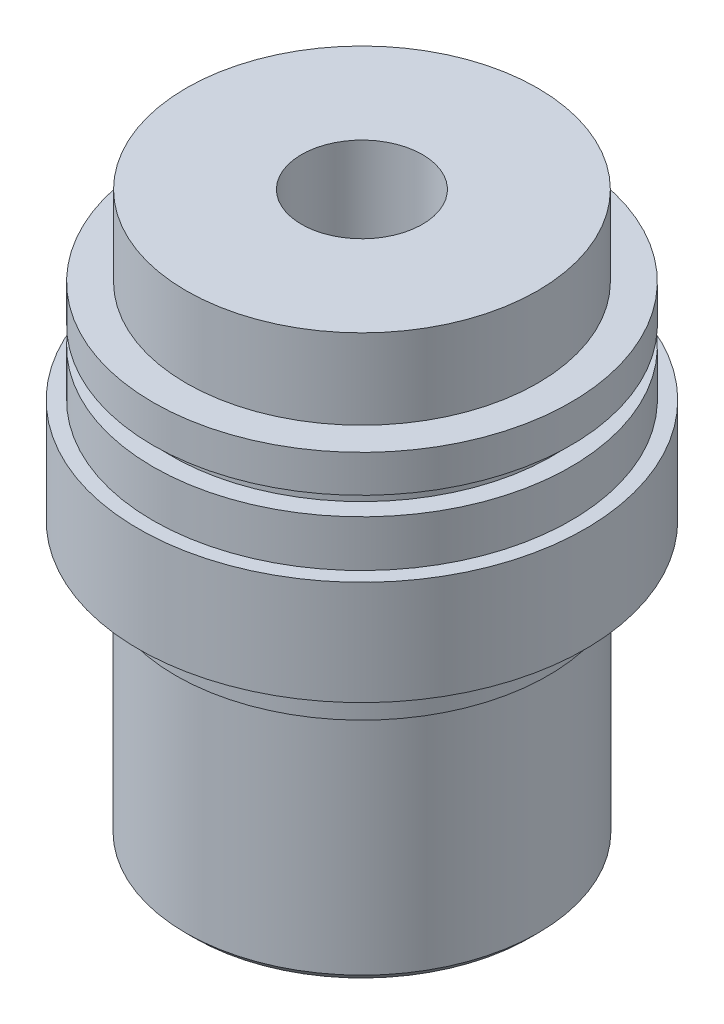
SolidWorks part; units mm, degrees
ref_plane "Front Plane" through (0, 0, 0) normal (0, 0, 1) x (1, 0, 0)
ref_plane "Top Plane" through (0, 0, 0) normal (0, 1, 0) x (1, 0, 0)
ref_plane "Right Plane" through (0, 0, 0) normal (1, 0, 0) x (0, 0, -1)
sketch "Sketch1" plane through (0, 0, 0) normal (0, 0, 1) x (1, 0, 0)
  line L0 (0, 0) -> (0, 30.33) construction
  line L1 (3.25, 0) -> (3.25, 30.33)
  line L2 (3.25, 30.33) -> (9.44, 30.33)
  line L3 (9.44, 30.33) -> (9.44, 26.03)
  line L4 (9.44, 26.03) -> (11.225, 26.03)
  line L5 (11.225, 26.03) -> (11.225, 24.03)
  line L6 (11.225, 24.03) -> (10.225, 24.03)
  line L7 (10.225, 24.03) -> (10.225, 23.03)
  line L8 (10.225, 23.03) -> (11.225, 23.03)
  line L9 (11.225, 23.03) -> (11.225, 20.53)
  line L10 (11.225, 20.53) -> (12, 20.53)
  line L11 (12, 20.53) -> (12, 14.93)
  line L12 (12, 14.93) -> (10, 14.93)
  line L13 (10, 14.93) -> (10, 12.7)
  line L14 (10, 12.7) -> (9.46, 12.7)
  line L15 (9.46, 12.7) -> (9.46, 0)
  line L16 (9.46, 0) -> (3.25, 0)
  dimension "D1" = 30.33
  dimension "D2" = 18.88
  dimension "D3" = 22.45
  dimension "D4" = 1
  dimension "D5" = 4.3
  dimension "D6" = 2
  dimension "D7" = 2.5
  dimension "D8" = 5.6
  dimension "D9" = 2.23
  dimension "D10" = 18.92
  dimension "D11" = 20
  dimension "D12" = 24
  dimension "D13" = 6.5
revolve "Revolve1" add sketch "Sketch1" angle 360 about L0
thread "Thread1" pitch 0.3175 start angle 0, offset 0, length 2.5, pitch 0.794, diameter 18.88
ref_plane "Plane1" through (-9.44, 30.33, 0) normal (0, 0, 1) x (-1, 0, 0)
sketch "Thread Profile1" plane through (-9.44, 30.33, 0) normal (0, 0, 1) x (-1, 0, 0)
  line L0 (0, 0) -> (0, 0.3175) construction
  line L1 (0, 0) -> (0.1719, 0.0992)
  line L2 (0.1719, 0.0992) -> (0.1719, 0.1389)
  line L3 (0.1719, 0.1389) -> (0, 0.2381)
  line L4 (0.1719, 0.1191) -> (0, 0.1191) construction
  line L11 (0, 0) -> (0, 0.2381)
  point P2 (0, 0)
  dimension "Pitch" = 0.3175
  dimension "Profile_Angle" = 60
  dimension "Profile_Land" = 0.0397
  dimension "Profile_Height" = 0.1719
chamfer "Chamfer1" distance 0.45 angle 45 3 edges at (0, 14.93, -10) (0, 0, -9.46) (0, 0, -3.25)
